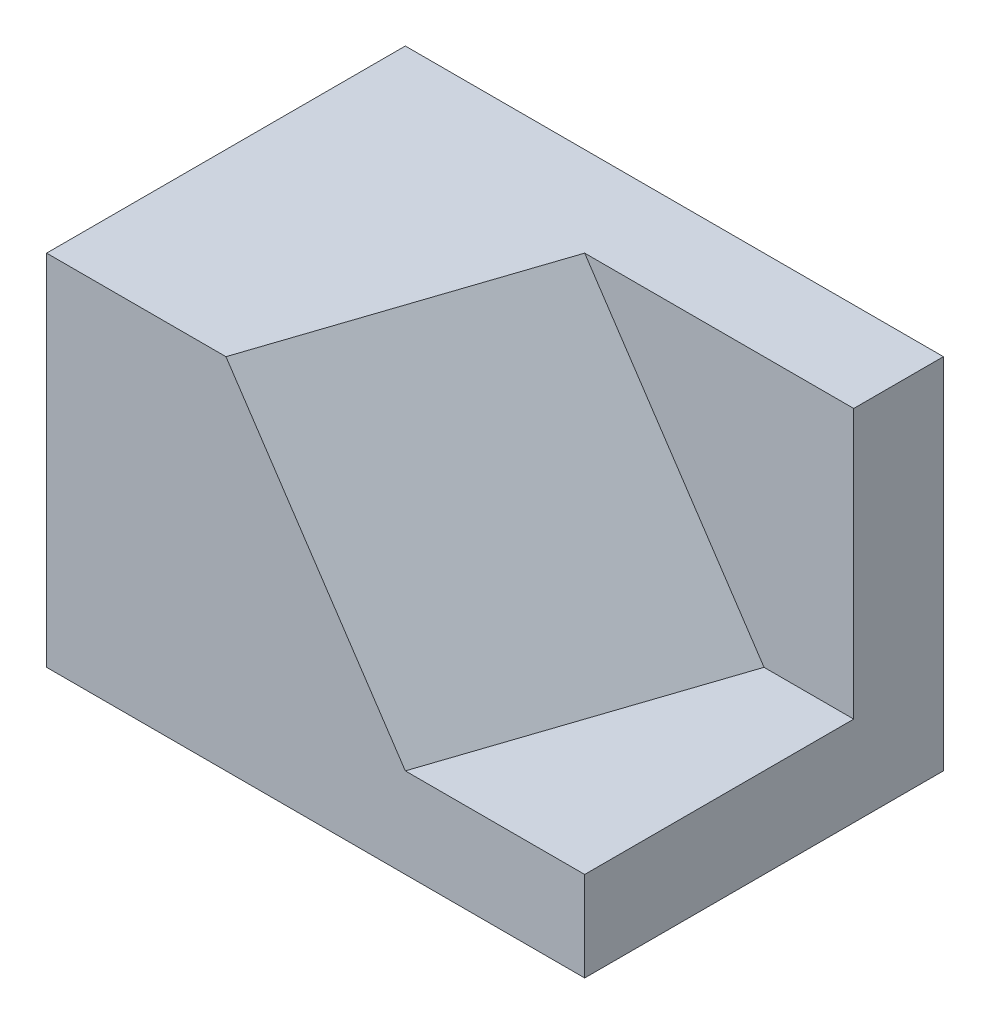
SolidWorks part; units mm, degrees
ref_plane "前基準面" through (0, 0, 0) normal (0, 0, 1) x (1, 0, 0)
ref_plane "上基準面" through (0, 0, 0) normal (0, 1, 0) x (1, 0, 0)
ref_plane "右基準面" through (0, 0, 0) normal (1, 0, 0) x (0, 0, -1)
sketch "草圖1" plane through (0, 0, 0) normal (0, 1, 0) x (1, 0, 0)
  line L1 (15, 10) -> (-15, 10)
  line L2 (15, 10) -> (15, -10)
  line L3 (15, -10) -> (-15, -10)
  line L4 (-15, 10) -> (-15, -10)
  line L5 (15, 10) -> (-15, -10) construction
  line L6 (15, -10) -> (-15, 10) construction
  point P0 (0, 0)
  dimension "D1" = 20
  dimension "D2" = 30
extrude "填料-伸長1" add sketch "草圖1" along normal blind 20
sketch "草圖2" plane through (0, 0, 10) normal (0, 0, 1) x (1, 0, 0)
  line L0 (-5, 20) -> (5, 5)
  line L1 (5, 5) -> (15, 5)
  line L2 (15, 20) -> (15, 0) construction
  line L3 (15, 5) -> (10, 5)
  line L4 (10, 5) -> (0, 20)
  line L5 (-15, 20) -> (15, 20) construction
  line L6 (-15, 0) -> (15, 0) construction
  point P11 (-5, 20)
  dimension "D1" = 5
  dimension "D2" = 10
  dimension "D3" = 5
  dimension "D4" = 15
  dimension "D5" = 5
sketch "草圖3" plane through (0, 20, 0) normal (0, 1, 0) x (1, 0, 0)
  line L0 (-5, -10) -> (0, 5)
  line L1 (-5, -10) -> (5, -10) construction
  line L2 (-15, -10) -> (15, -10) construction
  line L3 (0, 5) -> (15, 5)
  line L4 (15, -10) -> (15, 10) construction
  line L5 (15, 5) -> (10, 5)
  line L6 (10, 5) -> (5, -10)
  line L7 (15, 10) -> (-15, 10) construction
  dimension "D1" = 5
  dimension "D2" = 5
  dimension "D3" = 10
  dimension "D4" = 10
  dimension "D5" = 10
ref_plane "平面1" through (7.5, 5, 2.5) normal (-0.8018, -0.5345, -0.2673) x (-0.2224, -0.1482, 0.9636)
sketch "草圖6" plane through (7.5, 5, 2.5) normal (-0.8018, -0.5345, -0.2673) x (-0.2224, -0.1482, 0.9636)
  line L2 (7.7831, 19.4145) -> (7.7831, 1.3868) construction
  line L5 (7.7831, 19.4145) -> (-7.7831, 16.641) construction
  line L8 (7.7831, 19.4145) -> (7.7831, 1.3868)
  line L11 (7.7831, 19.4145) -> (-7.7831, 16.641)
  line L14 (7.7831, 1.3868) -> (-7.7831, 1.3868)
  line L15 (-7.7831, 1.3868) -> (-7.7831, 16.641)
sketch "草圖5" plane through (15, 0, 0) normal (1, 0, 0) x (0, 0, -1)
  line L0 (5, 20) -> (5, 5)
  line L1 (5, 20) -> (-10, 20) construction
  line L2 (-10, 20) -> (10, 20) construction
  line L3 (5, 5) -> (-10, 5)
  line L4 (-10, 5) -> (-10, 20) construction
  line L5 (-10, 0) -> (10, 0) construction
  line L6 (10, 20) -> (10, 0) construction
  line L7 (-10, 5) -> (-10, 20)
  line L8 (-10, 20) -> (-10, 5) construction
  line L9 (-10, 20) -> (5, 20) construction
  line L10 (-10, 20) -> (5, 20)
  dimension "D1" = 360
  dimension "D2" = 5
extrude "除料-伸長3" cut sketch "草圖5" against normal up to surface (20 mm away) up to plane "平面1"
